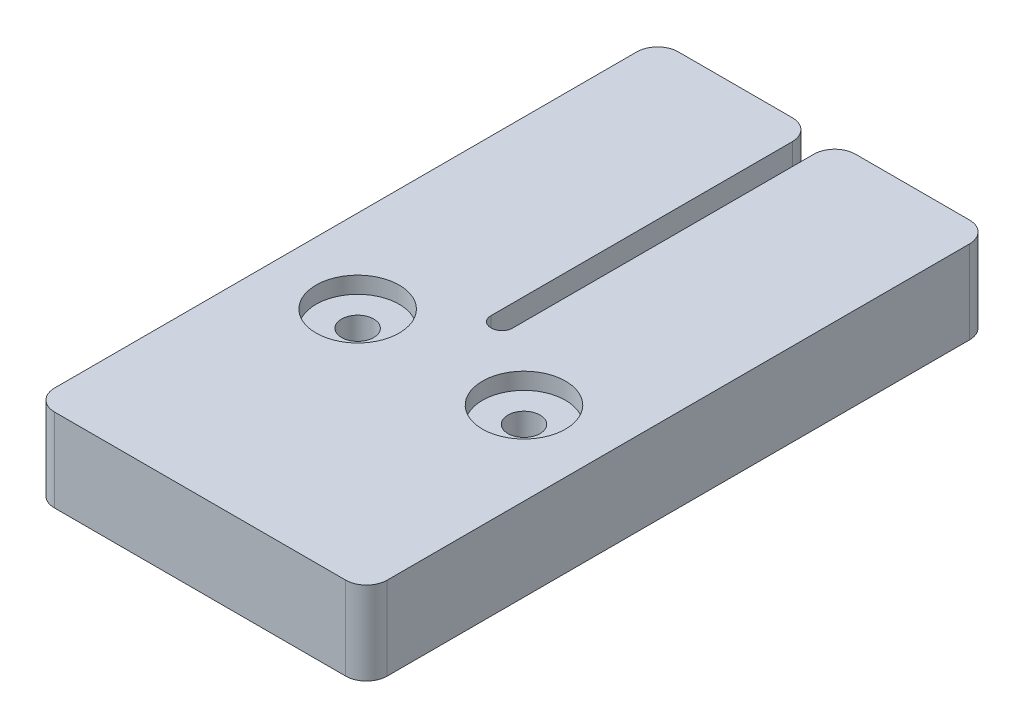
SolidWorks part; units mm, degrees
material "PE High Density"
ref_plane "Front Plane" through (0, 0, 0) normal (0, 0, 1) x (1, 0, 0)
ref_plane "Top Plane" through (0, 0, 0) normal (0, 1, 0) x (1, 0, 0)
ref_plane "Right Plane" through (0, 0, 0) normal (1, 0, 0) x (0, 0, -1)
sketch "Sketch1" plane through (0, 0, 0) normal (0, 1, 0) x (1, 0, 0)
  line L0 (-25.4, 0) -> (25.4, 0)
  line L1 (25.4, 0) -> (25.4, 95.25)
  line L2 (25.4, 95.25) -> (1.651, 95.25)
  line L5 (-1.651, 95.25) -> (-25.4, 95.25)
  line L6 (-25.4, 95.25) -> (-25.4, 0)
  line L7 (-1.651, 95.25) -> (-1.651, 44.45)
  line L8 (-1.651, 44.45) -> (1.651, 44.45)
  line L9 (1.651, 44.45) -> (1.651, 95.25)
  dimension "D1" = 50.8
  dimension "D2" = 95.25
  dimension "D3" = 3.302
  dimension "D4" = 50.8
extrude "Boss-Extrude1" add sketch "Sketch1" along normal blind 12.7
fillet "Fillet1" radius 3.175 6 edges at (1.651, 6.35, -95.25) (-1.651, 6.35, -95.25) (-25.4, 6.35, -95.25) (25.4, 6.35, -95.25) (-25.4, 6.35, 0) (25.4, 6.35, 0)
fillet "Fillet2" radius 1.5875 2 edges at (-1.651, 6.35, -44.45) (1.651, 6.35, -44.45)
sketch "Sketch2" plane through (0, 0, 0) normal (0, -1, 0) x (1, 0, 0)
  line L0 (-22.225, 0) -> (22.225, 0) construction
  circle A0 centre (-12.7, -36.7538) radius 2.4575
  circle A1 centre (12.7, -36.7538) radius 2.4575
  dimension "D1" = 4.9149
  dimension "D2" = 36.7538
  dimension "D3" = 12.7
  dimension "D4" = 12.7
extrude "Cut-Extrude1" cut sketch "Sketch2" against normal through all
sketch "Sketch3" plane through (0, 12.7, 0) normal (0, 1, 0) x (1, 0, 0)
  circle A0 centre (12.7, 36.7538) radius 6.35
  circle A1 centre (-12.7, 36.7538) radius 6.35
  circle A2 centre (-12.7, 36.7538) radius 2.4575 construction
  circle A3 centre (12.7, 36.7538) radius 2.4575 construction
  dimension "D1" = 12.7
extrude "Cut-Extrude2" cut sketch "Sketch3" against normal blind 2.54
